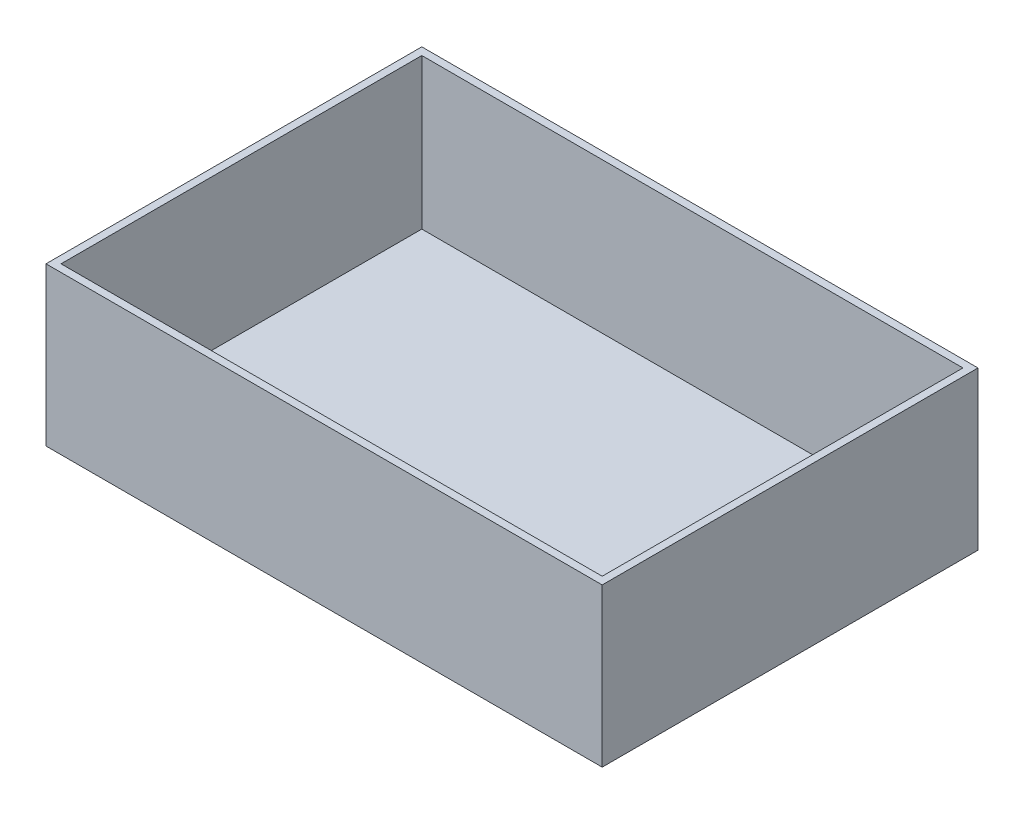
SolidWorks part; units mm, degrees
ref_plane "Front Plane" through (0, 0, 0) normal (0, 0, 1) x (1, 0, 0)
ref_plane "Top Plane" through (0, 0, 0) normal (0, 1, 0) x (1, 0, 0)
ref_plane "Right Plane" through (0, 0, 0) normal (1, 0, 0) x (0, 0, -1)
sketch "Sketch1" plane through (0, 0, 0) normal (0, 1, 0) x (1, 0, 0)
  line L0 (-180, 0) -> (-185, 0) construction
  line L1 (-180, 120) -> (180, 120)
  line L2 (-180, 120) -> (-180, -120)
  line L3 (-180, -120) -> (180, -120)
  line L4 (180, 120) -> (180, -120)
  line L5 (-180, 120) -> (180, -120) construction
  line L6 (-180, -120) -> (180, 120) construction
  line L7 (-185, 125) -> (185, 125)
  line L8 (-185, 125) -> (-185, -125)
  line L9 (-185, -125) -> (185, -125)
  line L10 (185, 125) -> (185, -125)
  line L11 (-185, 125) -> (185, -125) construction
  line L12 (-185, -125) -> (185, 125) construction
  point P0 (0, 0)
  point P6 (0, 0)
  dimension "D1" = 370
  dimension "D2" = 250
  dimension "D3" = 360
  dimension "D4" = 240
extrude "Boss-Extrude1" add sketch "Sketch1" along normal blind 100
sketch "Sketch2" plane through (0, 0, 0) normal (0, -1, 0) x (1, 0, 0)
  line L4 (185, -125) -> (185, 125)
  line L5 (185, 125) -> (-185, 125)
  line L6 (-185, 125) -> (-185, -125)
  line L7 (-185, -125) -> (185, -125)
  line L8 (185, -125) -> (185, 125)
  line L9 (185, 125) -> (-185, 125)
  line L10 (-185, 125) -> (-185, -125)
  line L11 (-185, -125) -> (185, -125)
  dimension "D1" = 0
extrude "Boss-Extrude2" add sketch "Sketch2" along normal blind 5
